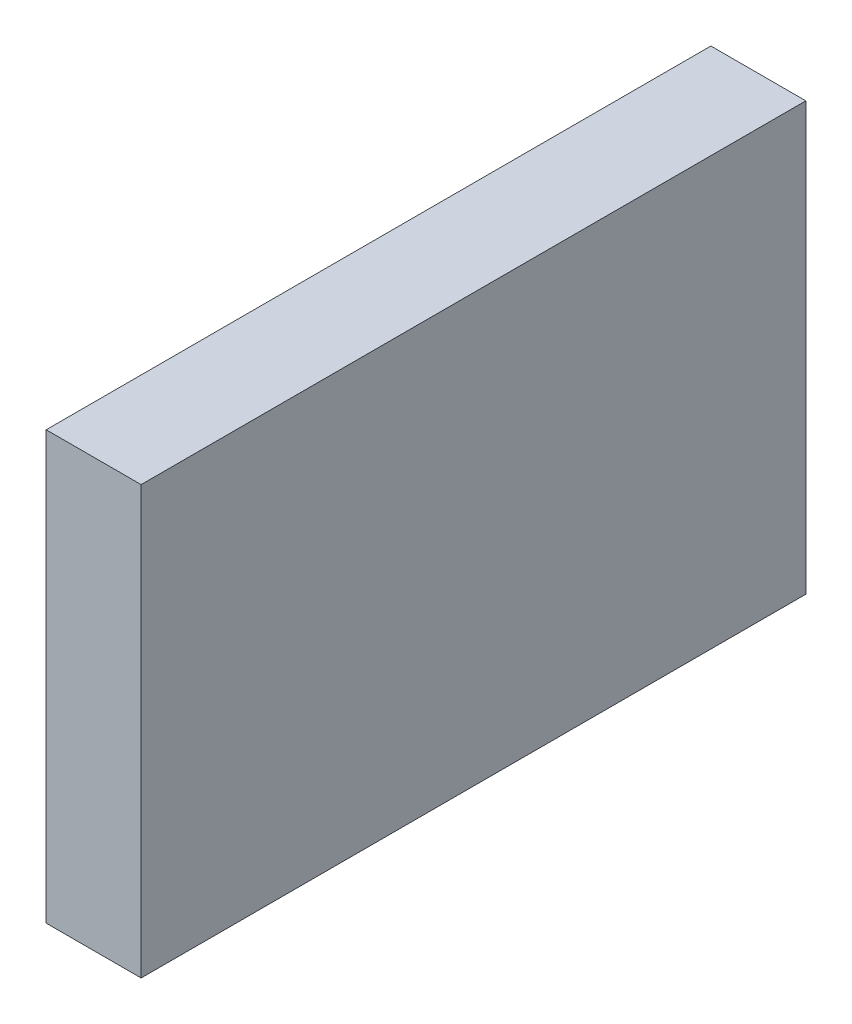
SolidWorks part; units mm, degrees
ref_plane "Front Plane" through (0, 0, 0) normal (0, 0, 1) x (1, 0, 0)
ref_plane "Top Plane" through (0, 0, 0) normal (0, 1, 0) x (1, 0, 0)
ref_plane "Right Plane" through (0, 0, 0) normal (1, 0, 0) x (0, 0, -1)
sketch "Sketch1" plane through (0, 0, 0) normal (1, 0, 0) x (0, 0, -1)
  line L1 (-3.0187, 1.9317) -> (3.9813, 1.9317)
  line L2 (-3.0187, 1.9317) -> (-3.0187, -2.5683)
  line L3 (-3.0187, -2.5683) -> (3.9813, -2.5683)
  line L4 (3.9813, 1.9317) -> (3.9813, -2.5683)
  dimension "D1" = 7
  dimension "D2" = 4.5
extrude "Boss-Extrude1" add sketch "Sketch1" along normal blind 1
